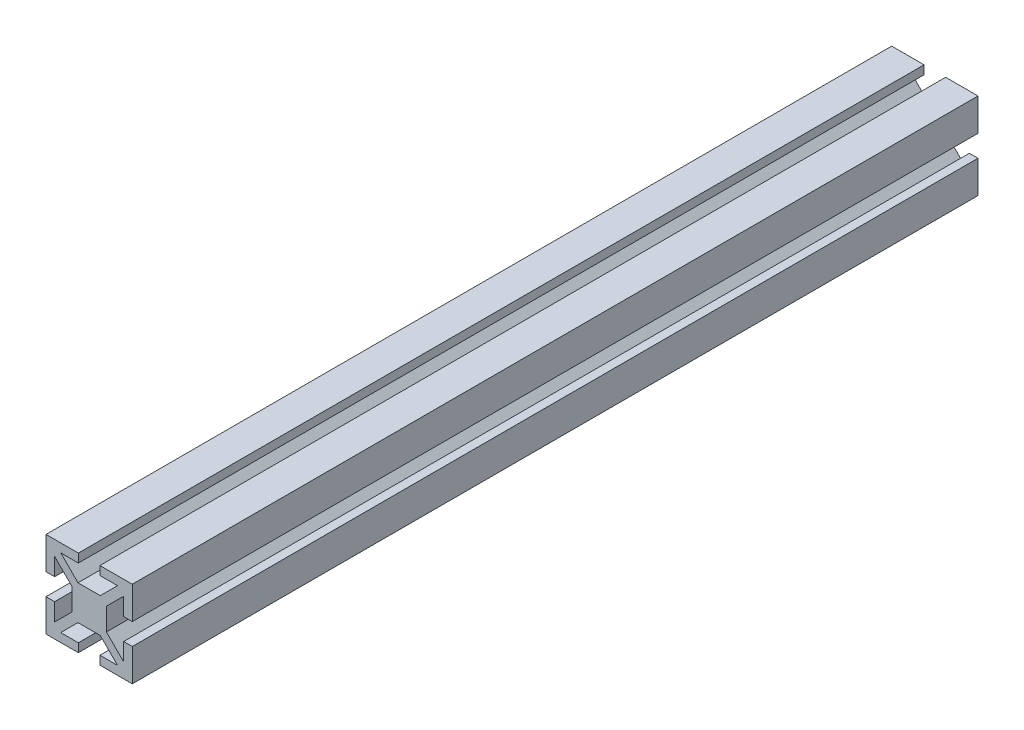
SolidWorks part; units mm, degrees
ref_plane "Front Plane" through (0, 0, 0) normal (0, 0, 1) x (1, 0, 0)
ref_plane "Top Plane" through (0, 0, 0) normal (0, 1, 0) x (1, 0, 0)
ref_plane "Right Plane" through (0, 0, 0) normal (1, 0, 0) x (0, 0, -1)
sketch "Sketch1" plane through (0, 0, 0) normal (0, 0, 1) x (1, 0, 0)
  line L0 (0, 4) -> (0, -4) construction
  line L1 (-2.5858, 4) -> (2.5858, 4)
  line L2 (-4, 2.5858) -> (-4, -2.5858)
  line L5 (-10, 10) -> (0, 0) construction
  line L6 (0, 10) -> (0, 4) construction
  line L7 (-4, 2.5858) -> (-8, 6.5858)
  line L8 (-6.5858, 8) -> (-2.5, 8)
  line L9 (-2.5, 8) -> (-2.5, 10)
  line L10 (-2.5, 10) -> (-10, 10)
  line L11 (-10, 10) -> (-10, 2.5)
  line L12 (-10, 2.5) -> (-8, 2.5)
  line L13 (-8, 2.5) -> (-8, 6.5858)
  line L14 (-4, 0) -> (4, 0) construction
  line L15 (-4, 0) -> (-10, 0) construction
  line L16 (-2.5858, 4) -> (-6.5858, 8)
  line L17 (-10, -10) -> (0, 0) construction
  line L18 (-2.5858, -4) -> (-6.5858, -8)
  line L19 (-8, -2.5) -> (-8, -6.5858)
  line L20 (-10, -2.5) -> (-8, -2.5)
  line L21 (-10, -10) -> (-10, -2.5)
  line L22 (-2.5, -10) -> (-10, -10)
  line L23 (-2.5, -8) -> (-2.5, -10)
  line L24 (-6.5858, -8) -> (-2.5, -8)
  line L25 (-4, -2.5858) -> (-8, -6.5858)
  line L26 (-2.5858, -4) -> (2.5858, -4)
  line L27 (10, -10) -> (0, 0) construction
  line L28 (4, 0) -> (10, 0) construction
  line L29 (10, 10) -> (0, 0) construction
  line L30 (4, -2.5858) -> (8, -6.5858)
  line L31 (6.5858, -8) -> (2.5, -8)
  line L32 (2.5, -8) -> (2.5, -10)
  line L33 (2.5, -10) -> (10, -10)
  line L34 (10, -10) -> (10, -2.5)
  line L35 (10, -2.5) -> (8, -2.5)
  line L36 (8, -2.5) -> (8, -6.5858)
  line L37 (2.5858, -4) -> (6.5858, -8)
  line L38 (2.5858, 4) -> (6.5858, 8)
  line L39 (8, 2.5) -> (8, 6.5858)
  line L40 (10, 2.5) -> (8, 2.5)
  line L41 (10, 10) -> (10, 2.5)
  line L42 (2.5, 10) -> (10, 10)
  line L43 (2.5, 8) -> (2.5, 10)
  line L44 (6.5858, 8) -> (2.5, 8)
  line L45 (4, 2.5858) -> (8, 6.5858)
  line L46 (4, 2.5858) -> (4, -2.5858)
  point P0 (0, 0)
  dimension "D1" = 10
  dimension "D2" = 4
  dimension "D3" = 2
  dimension "D4" = 10
  dimension "D5" = 2
  dimension "D6" = 2.5
  dimension "D7" = 2.5
  dimension "D8" = 4
  dimension "D9" = 1
  dimension "D10" = 1
extrude "Boss-Extrude1" add sketch "Sketch1" along normal mid plane 196
sketch "Sketch2" plane through (4, 0, 0) normal (1, 0, 0) x (0, 0, -1)
  line L0 (98, -2.5858) -> (98, 2.5858) construction
  line L1 (0, 10) -> (0, -10) construction
  line L2 (-98, 10) -> (98, 10) construction
  line L3 (-98, -10) -> (98, -10) construction
  circle A0 centre (88, 0) radius 2.5
  circle A1 centre (-88, 0) radius 2.5
  dimension "D1" = 5
  dimension "D2" = 10
extrude "Cut-Extrude1" cut sketch "Sketch2" against normal blind 8
